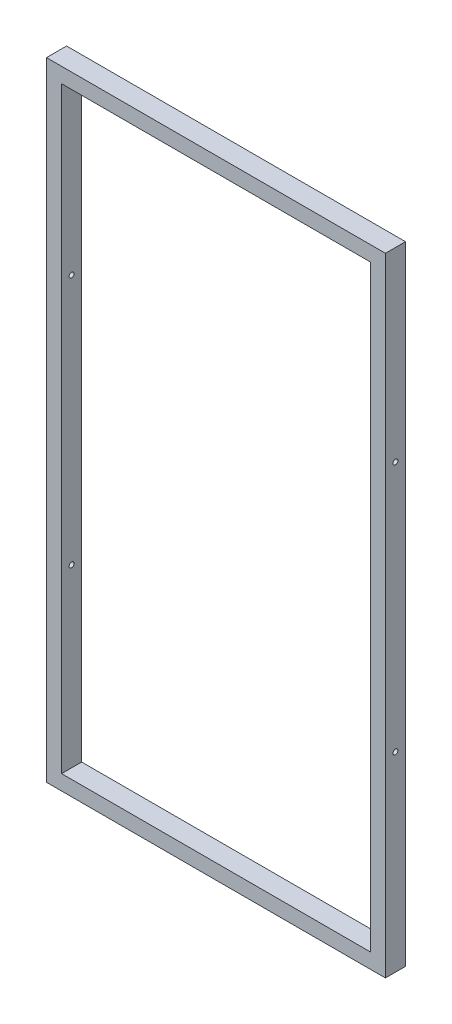
SolidWorks part; units mm, degrees
ref_plane "Спереди" through (0, 0, 0) normal (0, 0, 1) x (1, 0, 0)
ref_plane "Сверху" through (0, 0, 0) normal (0, 1, 0) x (1, 0, 0)
ref_plane "Справа" through (0, 0, 0) normal (1, 0, 0) x (0, 0, -1)
sketch "Эскиз2" plane through (0, 0, 0) normal (0, 0, 1) x (1, 0, 0)
  line L0 (-40.6984, 1181.1315) -> (-40.6984, -8.8685)
  line L1 (-40.6984, -8.8685) -> (574.3016, -8.8685)
  line L2 (574.3016, -8.8685) -> (574.3016, 1181.1315)
  line L3 (574.3016, 1181.1315) -> (-40.6984, 1181.1315)
  line L4 (-70.6984, 1211.1315) -> (-70.6984, -38.8685)
  line L5 (-70.6984, -38.8685) -> (604.3016, -38.8685)
  line L6 (604.3016, -38.8685) -> (604.3016, 1211.1315)
  line L7 (604.3016, 1211.1315) -> (-70.6984, 1211.1315)
  dimension "D1" = 30
  dimension "D2" = 30
  dimension "D3" = 615
  dimension "D4" = 30
  dimension "D5" = 30
  dimension "D6" = 1250
extrude "Главная жердь" add sketch "Эскиз2" along normal blind 40
sketch "Эскиз3" plane through (604.3016, 0, 0) normal (1, 0, 0) x (0, 0, -1)
  line L0 (-40, 841.1315) -> (0, 841.1315) construction
  line L1 (-40, -38.8685) -> (-40, 1211.1315) construction
  line L2 (0, -38.8685) -> (0, 1211.1315) construction
  line L4 (-40, 341.1315) -> (0, 341.1315) construction
  line L5 (-40, -38.8685) -> (0, -38.8685) construction
  circle A0 centre (-20, 841.1315) radius 5
  circle A1 centre (-20, 341.1315) radius 5
  point P14 (-20, -38.8685)
  dimension "D1" = 10
  dimension "D3" = 10
  dimension "D4" = 380
  dimension "D5" = 500
extrude "Вырез-Вытянуть1" cut sketch "Эскиз3" against normal through all
